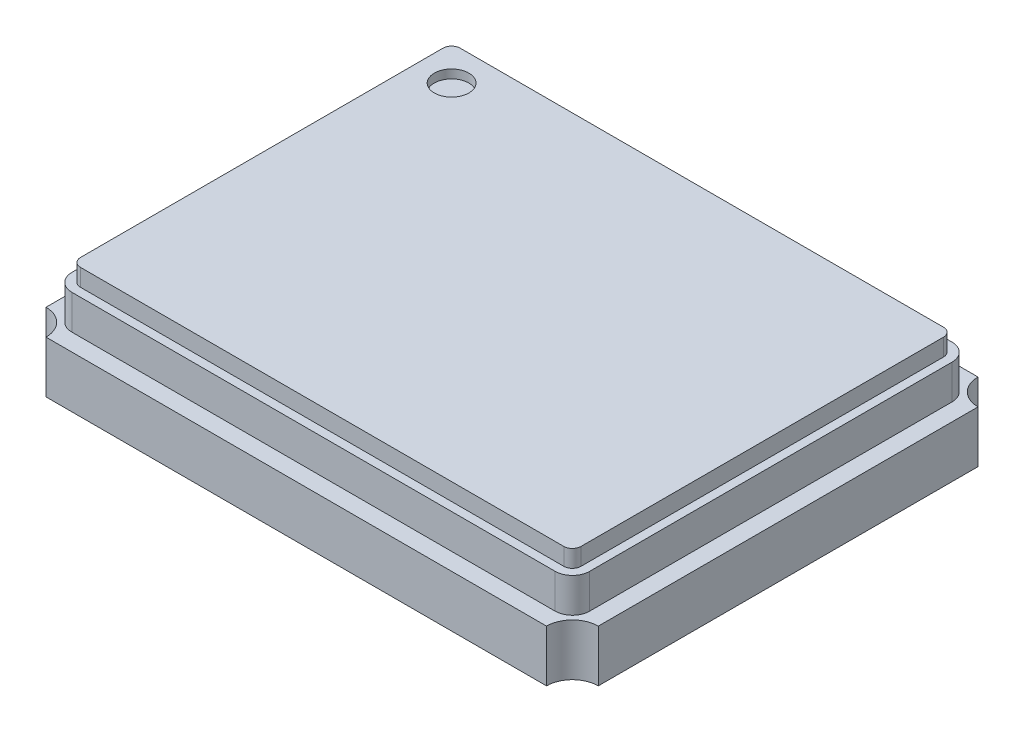
SolidWorks part; units mm, degrees
ref_plane "Front Plane" through (0, 0, 0) normal (0, 0, 1) x (1, 0, 0)
ref_plane "Top Plane" through (0, 0, 0) normal (0, 1, 0) x (1, 0, 0)
ref_plane "Right Plane" through (0, 0, 0) normal (1, 0, 0) x (0, 0, -1)
sketch "Sketch1" plane through (0, 0, 0) normal (0, 1, 0) x (1, 0, 0)
  line L1 (-1.6, -1.25) -> (1.6, -1.25)
  line L2 (-1.6, -1.25) -> (-1.6, 1.25)
  line L3 (-1.6, 1.25) -> (1.6, 1.25)
  line L4 (1.6, -1.25) -> (1.6, 1.25)
  line L5 (-1.6, -1.25) -> (1.6, 1.25) construction
  line L6 (-1.6, 1.25) -> (1.6, -1.25) construction
  point P0 (0, 0)
  dimension "D1" = 3.2
  dimension "D2" = 2.5
extrude "Boss-Extrude1" add sketch "Sketch1" along normal blind 0.3
sketch "Sketch2" plane through (0, 0.3, 0) normal (0, 1, 0) x (1, 0, 0)
  line L0 (1.6, 1.25) -> (-1.6, 1.25) construction
  line L1 (-1.4, -1.15) -> (1.4, -1.15)
  line L2 (-1.5, -1.05) -> (-1.5, 1.05)
  line L3 (-1.4, 1.15) -> (1.4, 1.15)
  line L4 (1.5, -1.05) -> (1.5, 1.05)
  line L5 (-1.5, -1.15) -> (1.5, 1.15) construction
  line L6 (-1.5, 1.15) -> (1.5, -1.15) construction
  line L7 (1.6, -1.25) -> (1.6, 1.25) construction
  arc A0 (-1.4, -1.15) -> (-1.5, -1.05) centre (-1.4, -1.05) cw
  arc A1 (1.4, -1.15) -> (1.5, -1.05) centre (1.4, -1.05) ccw
  arc A2 (1.4, 1.15) -> (1.5, 1.05) centre (1.4, 1.05) cw
  arc A3 (-1.5, 1.05) -> (-1.4, 1.15) centre (-1.4, 1.05) cw
  point P0 (0, 0)
  dimension "D3" = 0.1
  dimension "D1" = 0.1
  dimension "D2" = 0.1
extrude "Boss-Extrude2" add sketch "Sketch2" along normal blind 0.2
sketch "Sketch3" plane through (0, 0.5, 0) normal (0, 1, 0) x (1, 0, 0)
  line L0 (1.4, 1.15) -> (-1.4, 1.15) construction
  line L1 (-1.4, -1.1) -> (1.4, -1.1)
  line L2 (-1.45, -1.05) -> (-1.45, 1.05)
  line L3 (-1.4, 1.1) -> (1.4, 1.1)
  line L4 (1.45, -1.05) -> (1.45, 1.05)
  line L5 (-1.45, -1.1) -> (1.45, 1.1) construction
  line L6 (-1.45, 1.1) -> (1.45, -1.1) construction
  line L7 (-1.5, 1.05) -> (-1.5, -1.05) construction
  arc A0 (1.4, 1.1) -> (1.45, 1.05) centre (1.4, 1.05) cw
  arc A1 (1.4, -1.1) -> (1.45, -1.05) centre (1.4, -1.05) ccw
  arc A2 (-1.4, -1.1) -> (-1.45, -1.05) centre (-1.4, -1.05) cw
  arc A3 (-1.45, 1.05) -> (-1.4, 1.1) centre (-1.4, 1.05) cw
  point P0 (0, 0)
  dimension "D3" = 0.05
  dimension "D1" = 0.05
  dimension "D2" = 0.05
extrude "Boss-Extrude3" add sketch "Sketch3" along normal blind 0.1
sketch "Sketch4" plane through (0, 0.3, 0) normal (0, 1, 0) x (1, 0, 0)
  line L0 (0, 1.25) -> (0, -1.25) construction
  line L1 (1.6, 1.25) -> (-1.6, 1.25) construction
  line L2 (-1.6, -1.25) -> (1.6, -1.25) construction
  line L3 (-1.6, 0) -> (1.6, 0) construction
  line L4 (-1.6, 1.25) -> (-1.6, -1.25) construction
  line L5 (1.6, -1.25) -> (1.6, 1.25) construction
  circle A0 centre (-1.6, 1.25) radius 0.15
  circle A1 centre (1.6, 1.25) radius 0.15
  circle A2 centre (1.6, -1.25) radius 0.15
  circle A3 centre (-1.6, -1.25) radius 0.15
  dimension "D1" = 0.3
extrude "Cut-Extrude1" cut sketch "Sketch4" against normal through all
sketch "Sketch5" plane through (0, 0.6, 0) normal (0, 1, 0) x (1, 0, 0)
  line L0 (1.4, 1.1) -> (-1.4, 1.1) construction
  line L1 (-1.45, 1.05) -> (-1.45, -1.05) construction
  circle A0 centre (-1.25, 0.9) radius 0.1
  dimension "D1" = 0.2
  dimension "D2" = 0.2
  dimension "D3" = 0.2
extrude "Cut-Extrude2" cut sketch "Sketch5" against normal blind 0.05
